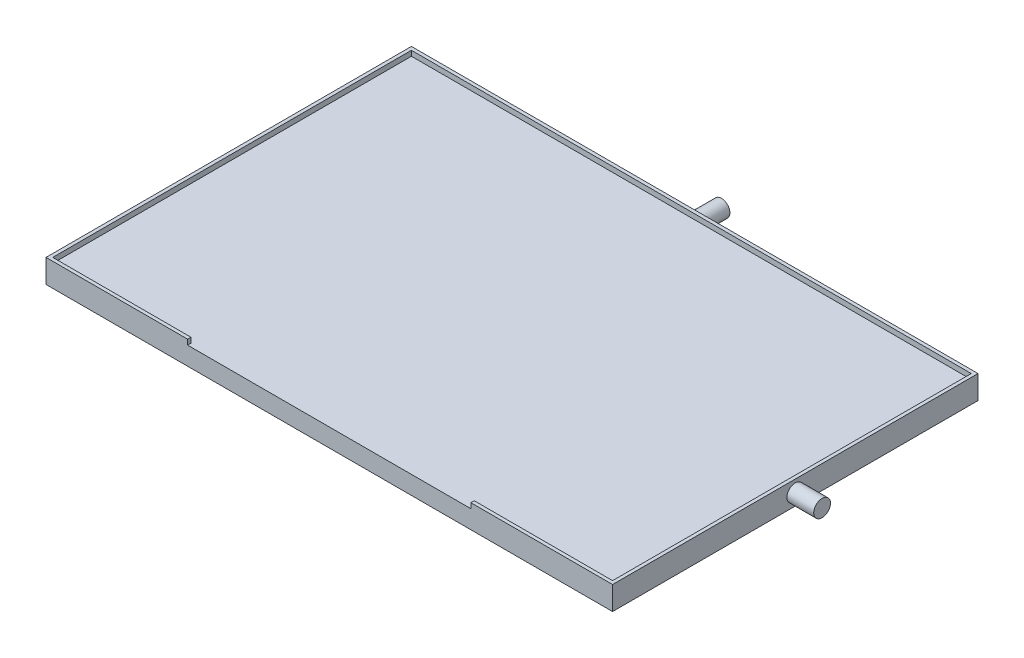
SolidWorks part; units mm, degrees
other "Markup1"
sketch "Sketch7" plane through (0, 7, 0) normal (-0.6577, 0.7171, 0.2306) x (0.3452, 0.0148, 0.9384)
ref_plane "Front Plane" through (0, 0, 0) normal (0, 0, 1) x (1, 0, 0)
ref_plane "Top Plane" through (0, 0, 0) normal (0, 1, 0) x (1, 0, 0)
ref_plane "Right Plane" through (0, 0, 0) normal (1, 0, 0) x (0, 0, -1)
sketch "Sketch1" plane through (0, 0, 0) normal (0, 0, 1) x (1, 0, 0)
  line L1 (0, 0) -> (169, 0)
  line L2 (0, 0) -> (0, 7)
  line L3 (0, 7) -> (169, 7)
  line L4 (169, 0) -> (169, 7)
  dimension "D1" = 169
  dimension "D2" = 7
extrude "Boss-Extrude1" add sketch "Sketch1" against normal blind 109
sketch "Sketch3" plane through (0, 7, 0) normal (0, 1, 0) x (1, 0, 0)
  line L0 (169, 0) -> (0, 0) construction
  line L1 (167, 2) -> (2, 2)
  line L2 (167, 2) -> (167, 107)
  line L3 (167, 107) -> (2, 107)
  line L4 (2, 2) -> (2, 107)
  line L5 (167, 2) -> (2, 107) construction
  line L6 (167, 107) -> (2, 2) construction
  line L7 (169, 109) -> (169, 0) construction
  point P0 (84.5, 54.5)
  dimension "D1" = 54.5
  dimension "D2" = 84.5
  dimension "D3" = 165
  dimension "D4" = 105
extrude "Cut-Extrude2" cut sketch "Sketch3" against normal blind 1.5
sketch "Sketch4" plane through (0, 0, 0) normal (0, 0, 1) x (1, 0, 0)
  line L0 (169, 7) -> (0, 7) construction
  line L1 (42.25, 7) -> (126.75, 7)
  line L2 (42.25, 7) -> (42.25, 5.45)
  line L3 (42.25, 5.45) -> (126.75, 5.45)
  line L4 (126.75, 7) -> (126.75, 5.45)
  line L5 (0, 7) -> (0, 0) construction
  dimension "D1" = 84.5
  dimension "D2" = 1.55
  dimension "D3" = 42.25
extrude "Cut-Extrude3" cut sketch "Sketch4" against normal blind 2
sketch "Sketch5" plane through (169, 0, 0) normal (1, 0, 0) x (0, 0, -1)
  line L0 (0, 0) -> (0, 7) construction
  line L1 (109, 0) -> (0, 0) construction
  circle A0 centre (54.5, 3.5) radius 2.5
  dimension "D3" = 5
  dimension "D1" = 54.5
  dimension "D2" = 3.5
extrude "Boss-Extrude2" add sketch "Sketch5" along normal blind 8
sketch "Sketch6" plane through (0, 0, -109) normal (0, 0, -1) x (-1, 0, 0)
  line L0 (0, 0) -> (-169, 0) construction
  line L1 (0, 7) -> (0, 0) construction
  circle A0 centre (-84.5, 3.5) radius 2.5
  dimension "D3" = 5
  dimension "D1" = 3.5
  dimension "D2" = 84.5
extrude "Boss-Extrude3" add sketch "Sketch6" along normal blind 8
sketch "Sketch8" plane through (0, 0, 0) normal (0, -1, 0) x (1, 0, 0)
  line L0 (0, -54.5) -> (169, -54.5) construction
  line L1 (0, -109) -> (0, 0) construction
  line L2 (169, -109) -> (169, 0) construction
  line L3 (84.5, -109) -> (84.5, 0) construction
  line L4 (0, -109) -> (169, -109) construction
  line L5 (0, 0) -> (169, 0) construction
  line L7 (99.5, -62) -> (109.5, -62)
  line L8 (99.5, -62) -> (99.5, -47)
  line L9 (99.5, -47) -> (109.5, -47)
  line L10 (109.5, -62) -> (109.5, -47)
  line L11 (99.5, -62) -> (109.5, -47) construction
  line L12 (99.5, -47) -> (109.5, -62) construction
  line L13 (69.5, -62) -> (59.5, -62)
  line L14 (69.5, -62) -> (69.5, -47)
  line L15 (69.5, -47) -> (59.5, -47)
  line L16 (59.5, -62) -> (59.5, -47)
  line L17 (69.5, -62) -> (59.5, -47) construction
  line L18 (69.5, -47) -> (59.5, -62) construction
  point P12 (104.5, -54.5)
  point P17 (64.5, -54.5)
  point P22 (69.5, -54.5)
  point P23 (84.5, -54.5)
  dimension "D1" = 15
  dimension "D2" = 15
  dimension "D3" = 10
  dimension "D4" = 10
  dimension "D5" = 30
  dimension "D6" = 20
extrude "Boss-Extrude4" add sketch "Sketch8" along normal blind 10
sketch "Sketch9" plane through (69.5, 0, 0) normal (1, 0, 0) x (0, 0, -1)
  line L0 (62, -10) -> (47, -10) construction
  circle A0 centre (54.5, -10) radius 2.55
  dimension "D1" = 5.1
extrude "Cut-Extrude4" cut sketch "Sketch9" against normal blind 5.1 and the other way blind 35.1
sketch "Sketch10" plane through (0, 7, 0) normal (0, 1, 0) x (1, 0, 0)
  line L0 (126.75, 2) -> (167, 2) construction
  line L5 (167, 2) -> (167, 107) construction
  line L7 (1, 1) -> (168, 1)
  line L8 (1, 1) -> (1, 108)
  line L9 (1, 108) -> (168, 108)
  line L10 (168, 1) -> (168, 108)
  line L11 (1, 1) -> (168, 108) construction
  line L12 (1, 108) -> (168, 1) construction
  point P0 (84.5, 54.5)
  point P8 (84.5, 54.5)
  dimension "D1" = 52.5
  dimension "D2" = 82.5
  dimension "D3" = 167
  dimension "D4" = 107
extrude "Cut-Extrude5" cut sketch "Sketch10" against normal blind 1.55 contours L8 L7 L10 L9
